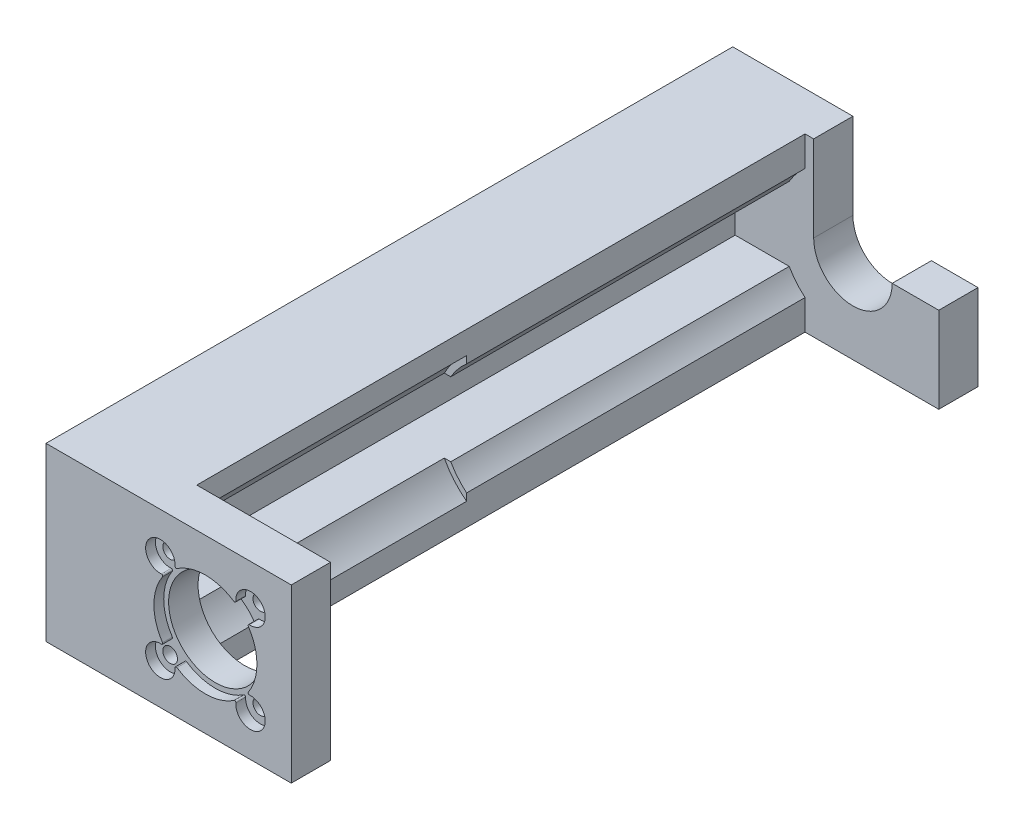
SolidWorks part; units mm, degrees
ref_plane "Piano frontale" through (0, 0, 0) normal (0, 0, 1) x (1, 0, 0)
ref_plane "Piano superiore" through (0, 0, 0) normal (0, 1, 0) x (1, 0, 0)
ref_plane "Piano destro" through (0, 0, 0) normal (1, 0, 0) x (0, 0, -1)
sketch "Sketch1" plane through (0, 0, 0) normal (0, 0, 1) x (1, 0, 0)
  line L0 (0, 17.5) -> (50, 17.5) construction
  line L1 (0, 0) -> (50, 0)
  line L2 (0, 0) -> (0, 35)
  line L3 (0, 35) -> (50, 35)
  line L4 (50, 0) -> (50, 35)
  line L5 (25, 35) -> (25, 0) construction
  line L6 (32.5, 17.5) -> (41.6924, 26.6924) construction
  line L7 (32.5, 17.5) -> (41.6924, 8.3076) construction
  line L8 (32.5, 17.5) -> (32.5, 0) construction
  line L9 (32.5, 17.5) -> (23.3076, 8.3076) construction
  line L10 (32.5, 17.5) -> (23.3076, 26.6924) construction
  circle A0 centre (32.5, 17.5) radius 9.5
  circle A1 centre (32.5, 17.5) radius 13 construction
  circle A2 centre (41.6924, 26.6924) radius 1.5
  circle A3 centre (41.6924, 8.3076) radius 1.5
  circle A4 centre (23.3076, 8.3076) radius 1.5
  circle A5 centre (23.3076, 26.6924) radius 1.5
  circle A6 centre (32.5, 17.5) radius 16 construction
  dimension "D2" = 19
  dimension "D4" = 26
  dimension "D6" = 3
  dimension "D7" = 17.5
  dimension "D9" = 32
  dimension "D1" = 50
  dimension "D3" = 17.5
  dimension "D5" = 45
  dimension "D8" = 35
extrude "Boss-Extrude3" add sketch "Sketch1" along normal blind 6
sketch "Sketch4" plane through (0, 0, 6) normal (0, 0, 1) x (1, 0, 0)
  line L0 (32.5, 17.5) -> (32.5, 34.7569) construction
  line L1 (32.5, 17.5) -> (32.5, 0) construction
  line L2 (0, 0) -> (50, 0) construction
  line L3 (32.5, 17.5) -> (0, 17.5) construction
  line L4 (0, 35) -> (0, 0) construction
  line L6 (0, 35) -> (50, 35)
  line L7 (0, 35) -> (0, 0)
  line L8 (0, 0) -> (50, 0)
  line L9 (50, 35) -> (50, 0)
  arc A0 (26.2994, 26.4708) -> (23.5292, 23.7006) centre (23.3076, 26.6924) ccw
  arc A1 (26.2994, 8.5292) -> (23.5292, 11.2994) centre (23.3076, 8.3076) cw
  arc A2 (38.7006, 8.5292) -> (41.4708, 11.2994) centre (41.6924, 8.3076) ccw
  arc A3 (38.7006, 26.4708) -> (41.4708, 23.7006) centre (41.6924, 26.6924) cw
  arc A4 (23.7558, 23.3129) -> (23.7558, 11.6871) centre (32.5, 17.5) ccw
  arc A5 (38.3129, 26.2442) -> (26.6871, 26.2442) centre (32.5, 17.5) ccw
  arc A6 (41.2442, 11.6871) -> (41.2442, 23.3129) centre (32.5, 17.5) ccw
  arc A7 (26.6871, 8.7558) -> (38.3129, 8.7558) centre (32.5, 17.5) ccw
  arc A8 (23.7558, 11.6871) -> (23.5292, 11.2994) centre (23.5476, 11.5487) cw
  arc A9 (26.6871, 8.7558) -> (26.2994, 8.5292) centre (26.5487, 8.5476) ccw
  arc A10 (38.3129, 8.7558) -> (38.7006, 8.5292) centre (38.4513, 8.5476) cw
  arc A11 (41.2442, 11.6871) -> (41.4708, 11.2994) centre (41.4524, 11.5487) ccw
  arc A12 (41.2442, 23.3129) -> (41.4708, 23.7006) centre (41.4524, 23.4513) cw
  arc A13 (38.3129, 26.2442) -> (38.7006, 26.4708) centre (38.4513, 26.4524) ccw
  arc A14 (26.6871, 26.2442) -> (26.2994, 26.4708) centre (26.5487, 26.4524) cw
  arc A15 (23.7558, 23.3129) -> (23.5292, 23.7006) centre (23.5476, 23.4513) ccw
  dimension "D1" = 6
  dimension "D2" = 21
  dimension "D3" = 0.25
extrude "Boss-Extrude5" add sketch "Sketch4" along normal blind 2
sketch "Sketch8" plane through (0, 0, 0) normal (0, 0, -1) x (-1, 0, 0)
  line L0 (-50, 35) -> (0, 35) construction
  line L1 (-22.7403, 35) -> (0, 35)
  line L2 (-22.7403, 35) -> (-22.7403, 30.3675)
  line L3 (-22.7403, 0) -> (0, 0)
  line L4 (0, 35) -> (0, 0)
  line L5 (-22.7403, 4.6325) -> (-22.7403, 0)
  line L6 (0, 35) -> (0, 0) construction
  line L7 (-16.35, 17.5) -> (-32.5, 17.5) construction
  line L8 (-8.5, 25) -> (-18.1947, 25)
  line L9 (0, 25) -> (0, 10)
  line L10 (-8.5, 10) -> (-18.1971, 10)
  line L11 (-18.1947, 25) -> (-18.1947, 24.9954)
  line L13 (0, 35) -> (-8.5, 35)
  line L14 (0, 35) -> (0, 0)
  line L15 (0, 0) -> (-8.5, 0)
  line L16 (-8.5, 25) -> (-8.5, 10)
  arc A0 (-22.7403, 4.6325) -> (-18.1971, 10) centre (-32.5, 17.5) ccw
  arc A1 (-18.1947, 24.9954) -> (-22.7403, 30.3675) centre (-32.5, 17.5) ccw
  line M3 (0, 0) -> (0, 35)
  line M4 (0, 35) -> (-50, 35)
  line M6 (-50, 0) -> (0, 0)
  dimension "D1" = 32.3
  dimension "D2" = 22.7403
  dimension "D3" = 15
  dimension "D4" = 18.1947
  dimension "D5" = 25
  dimension "D6" = 8.5
extrude "Boss-Extrude6" add sketch "Sketch8" along normal blind 55 contours A1 L11 L8 L16 L10 A0 L5 L3 L4 L1 L2 M6 M3 M4
sketch "Sketch9" plane through (0, 0, 0) normal (-1, 0, 0) x (0, 0, 1)
  line L0 (-55, 17.5) -> (8, 17.5) construction
  line L1 (-55, 0) -> (-55, 35) construction
  line L2 (8, 35) -> (8, 0) construction
  line L3 (-72, 17.5) -> (-9, 17.5) construction
  line L4 (-89, 17.5) -> (-26, 17.5) construction
  line L5 (-106, 17.5) -> (-43, 17.5) construction
  line L6 (-123, 17.5) -> (-60, 17.5) construction
  line L7 (-140, 17.5) -> (-77, 17.5) construction
  line L8 (-157, 17.5) -> (-94, 17.5) construction
  line L9 (-174, 17.5) -> (-111, 17.5) construction
  circle A0 centre (-7, 17.5) radius 2
  circle A1 centre (-24, 17.5) radius 2
  circle A2 centre (-41, 17.5) radius 2
  circle A3 centre (-58, 17.5) radius 2
  circle A4 centre (-75, 17.5) radius 2
  circle A5 centre (-92, 17.5) radius 2
  circle A6 centre (-109, 17.5) radius 2
  circle A8 centre (-126, 17.5) radius 2 [skipped]
  dimension "D1" = 4
  dimension "D2" = 15
  dimension "D3" = 8
sketch "Sketch13" plane through (0, 0, -55) normal (0, 0, -1) x (-1, 0, 0)
  line L0 (-8.5, 25) -> (-8.5, 10)
  line L1 (-8.5, 25) -> (-8.5, 10) construction
  line L2 (-8.5, 25) -> (-19.5096, 25)
  line L3 (-22.7403, 35) -> (-22.7403, 28.8907)
  line L4 (-8.5, 10) -> (-19.5096, 10)
  line L5 (-22.7403, 0) -> (-22.7403, 6.1093)
  line L6 (-22.7403, 35) -> (0, 35)
  line L7 (0, 35) -> (0, 0)
  line L8 (0, 0) -> (-22.7403, 0)
  line L9 (-8.5, 25) -> (-18.1947, 25) construction
  arc A0 (-19.5096, 25) -> (-22.7403, 28.8907) centre (-32.5, 17.5) ccw
  arc A1 (-22.7403, 6.1093) -> (-19.5096, 10) centre (-32.5, 17.5) ccw
  dimension "D1" = 30
  dimension "D2" = 15
extrude "Boss-Extrude9" add sketch "Sketch13" along normal blind 69
sketch "Sketch14" plane through (0, 0, -124) normal (0, 0, -1) x (-1, 0, 0)
  line L0 (-24.5, 17.5) -> (-24.5, 35)
  line L1 (-50, 35) -> (-22.7403, 35) construction
  line L2 (-24.5, 35) -> (0, 35)
  line L3 (0, 35) -> (0, 0)
  line L4 (0, 0) -> (-50, 0)
  line L5 (-50, 0) -> (-50, 17.5)
  line L6 (-50, 0) -> (-50, 35) construction
  line L7 (-50, 17.5) -> (-40.5, 17.5)
  arc A0 (-40.5, 17.5) -> (-24.5, 17.5) centre (-32.5, 17.5) ccw
  dimension "D1" = 16
  dimension "D2" = 24.5
extrude "Boss-Extrude10" add sketch "Sketch14" along normal blind 8
extrude "Cut-Extrude1" cut sketch "Sketch9" against normal blind 8.5
